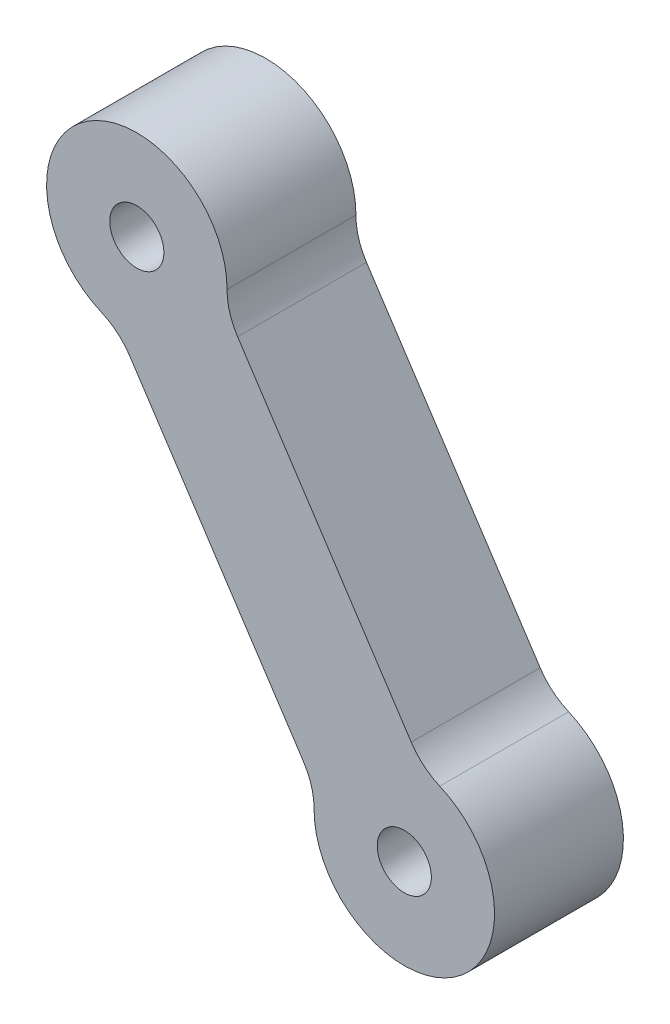
SolidWorks part; units mm, degrees
ref_plane "Alzado" through (0, 0, 0) normal (0, 0, 1) x (1, 0, 0)
ref_plane "Planta" through (0, 0, 0) normal (0, 1, 0) x (1, 0, 0)
ref_plane "Vista lateral" through (0, 0, 0) normal (1, 0, 0) x (0, 0, -1)
sketch "Croquis1" plane through (0, 0, 0) normal (0, 0, 1) x (1, 0, 0)
  line L0 (-32.291, 56.3417) -> (-18.8209, 35.8368)
  line L2 (-23.9331, 61.8321) -> (-10.463, 41.3272)
  arc A0 (-24.7541, 64.5997) -> (-34.505, 58.1941) centre (-31.754, 64.6309) ccw
  arc A2 (-8.249, 39.4748) -> (-17.9999, 33.0692) centre (-11, 33.038) cw
  arc A4 (-18.8209, 35.8368) -> (-17.9999, 33.0692) centre (-22.9999, 33.0915) cw
  arc A5 (-10.463, 41.3272) -> (-8.249, 39.4748) centre (-6.2841, 44.0725) ccw
  arc A6 (-24.7541, 64.5997) -> (-23.9331, 61.8321) centre (-19.7541, 64.5774) ccw
  circle A8 centre (-31.754, 64.6309) radius 2.1
  circle A9 centre (-11, 33.038) radius 2.1
  arc A10 (-34.505, 58.1941) -> (-32.291, 56.3417) centre (-36.4699, 53.5964) cw
  dimension "D1" = 4.2
extrude "Saliente-Extruir1" add sketch "Croquis1" along normal blind 10
